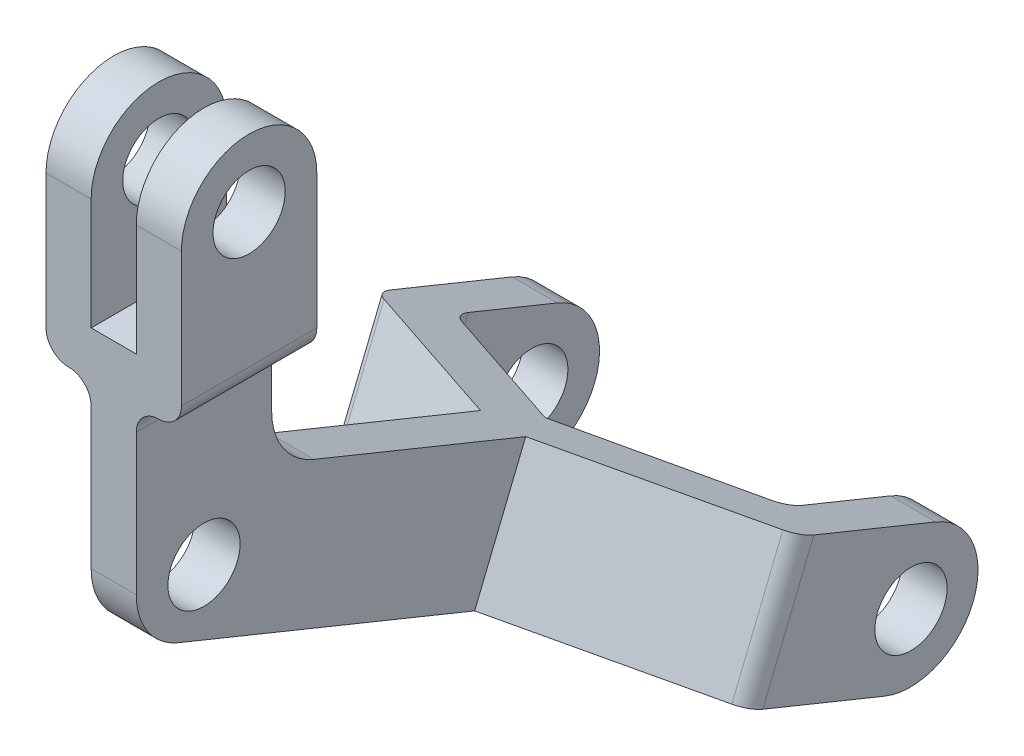
SolidWorks part; units mm, degrees
ref_plane "Front Plane" through (0, 0, 0) normal (0, 0, 1) x (1, 0, 0)
ref_plane "Top Plane" through (0, 0, 0) normal (0, 1, 0) x (1, 0, 0)
ref_plane "Right Plane" through (0, 0, 0) normal (1, 0, 0) x (0, 0, -1)
sketch "Sketch1" plane through (0, 0, 0) normal (1, 0, 0) x (0, 0, -1)
  line L0 (0, 0) -> (15, 0)
  line L2 (0, 0) -> (0, -15.9)
  line L3 (0, -15.9) -> (0, -15.59)
  line L4 (4.6728, -22.5367) -> (37.4848, -35.8904)
  line L5 (37.4848, -35.8904) -> (43.1391, -21.997)
  line L6 (43.1391, -21.997) -> (19.6728, -12.4467)
  line L8 (15, 0) -> (15, -5.5)
  arc A0 (0, -15.59) -> (4.6728, -22.5367) centre (7.5, -15.59) ccw
  arc A1 (19.6728, -12.4467) -> (15, -5.5) centre (22.5, -5.5) cw
  circle A2 centre (7.5, -16.4624) radius 4
  dimension "D3" = 7.5
  dimension "D4" = 7.5
  dimension "D9" = 8
  dimension "D1" = 15
  dimension "D2" = 15
  dimension "D5" = 5.5
  dimension "D6" = 15.59
  dimension "D7" = 6.7
  dimension "D8" = 7.5
extrude "Boss-Extrude1" add sketch "Sketch1" along normal blind 5 contours L6 A1 L8 L0 L2 A0 L4 L5 A2
sketch "Sketch2" plane through (0, 0, 0) normal (0, 0, 1) x (1, 0, 0)
  line L0 (0, 0) -> (5, 0)
  line L1 (5, 0) -> (5, -15.59) construction
  line L2 (10, 5) -> (10, 19.86)
  line L3 (10, 19.86) -> (5, 19.86)
  line L4 (5, 19.86) -> (5, 7.5)
  line L5 (5, 7.5) -> (0, 7.5)
  line L6 (0, 19.86) -> (0, 7.5)
  line L7 (2.5, 0) -> (2.5, 22.7767) construction
  line L8 (-5, 19.86) -> (0, 19.86)
  line L9 (-5, 5) -> (-5, 19.86)
  arc A0 (5, 0) -> (7.5, 2.5) centre (7.5, 0) cw
  arc A1 (7.5, 2.5) -> (10, 5) centre (7.5, 5) ccw
  arc A2 (-2.5, 2.5) -> (-5, 5) centre (-2.5, 5) cw
  arc A3 (0, 0) -> (-2.5, 2.5) centre (-2.5, 0) ccw
  point P22 (2.5, 7.5)
  dimension "D4" = 2.5
  dimension "D5" = 2.5
  dimension "D1" = 2.5
  dimension "D2" = 5
  dimension "D3" = 14.86
  dimension "D6" = 12.36
extrude "Boss-Extrude2" add sketch "Sketch2" against normal up to surface (15 mm away) up to face at (2.5, -2.75, -15)
sketch "Sketch3" plane through (10, 0, 0) normal (1, 0, 0) x (0, 0, -1)
  line L0 (0, 19.86) -> (27.8005, 19.86) construction
  line L2 (7.5, 5) -> (7.5, 19.86) construction
  line L3 (15, 5) -> (0, 5) construction
  circle A0 centre (7.5, 19.86) radius 7.5
  circle A1 centre (7.5, 19.86) radius 4
  dimension "D1" = 8
extrude "Boss-Extrude3" add sketch "Sketch3" against normal up to surface (5 mm away) up to face at (5, 13.68, -7.5)
sketch "Sketch5" plane through (10, 0, 0) normal (1, 0, 0) x (0, 0, -1)
  line L0 (11.5, 19.86) -> (3.5, 19.86) construction
  circle A0 centre (7.5, 19.86) radius 4
extrude "Cut-Extrude1" cut sketch "Sketch5" against normal blind 5
sketch "Sketch6" plane through (-5, 0, 0) normal (-1, 0, 0) x (0, 0, 1)
  line L0 (-15, 19.86) -> (0, 19.86) construction
  circle A0 centre (-7.5, 19.86) radius 7.5
extrude "Boss-Extrude4" add sketch "Sketch6" against normal up to surface (5 mm away) up to face at (0, 13.68, -7.5)
sketch "Sketch7" plane through (-5, 0, 0) normal (-1, 0, 0) x (0, 0, 1)
  circle A0 centre (-7.5, 19.86) radius 4
extrude "Cut-Extrude2" cut sketch "Sketch7" against normal blind 5
sketch "Sketch8" plane through (0, -3.8094, 1.5503) normal (0, 0.9262, -0.377) x (1, 0, 0)
  line L0 (0, 48.2487) -> (5, 48.2487)
  line L2 (0, 48.2487) -> (-19.6852, 57.9592)
  line L3 (-21.0793, 60.2013) -> (-21.0793, 74.7913)
  line L4 (-21.0793, 74.7913) -> (-16.0793, 74.7913)
  line L5 (-16.0793, 74.7913) -> (-16.0793, 64.1288)
  line L6 (-14.6852, 61.8867) -> (2.2583, 53.5287)
  line L7 (19.5563, 61.9014) -> (2.2583, 53.5287)
  line L8 (20.9211, 74.713) -> (20.9211, 64.1288)
  line L9 (25.9211, 74.713) -> (20.9211, 74.713)
  line L10 (25.9211, 60.123) -> (25.9211, 74.713)
  line L11 (5, 48.2487) -> (24.5563, 57.8956)
  arc A0 (-19.6852, 57.9592) -> (-21.0793, 60.2013) centre (-18.5793, 60.2013) cw
  arc A1 (-16.0793, 64.1288) -> (-14.6852, 61.8867) centre (-13.5793, 64.1288) ccw
  arc A2 (20.9211, 64.1288) -> (19.5563, 61.9014) centre (18.4211, 64.1288) cw
  arc A3 (24.5563, 57.8956) -> (25.9211, 60.123) centre (23.4211, 60.123) ccw
  dimension "D4" = 2.5
  dimension "D5" = 2.5
  dimension "D1" = 5
  dimension "D2" = 14.59
  dimension "D3" = 21.95
  dimension "D6" = 5.28
extrude "Boss-Extrude5" add sketch "Sketch8" against normal up to surface (15 mm away) up to face at (2.5, -29.2136, -21.0788)
sketch "Sketch9" plane through (25.9211, 0, 0) normal (1, 0, 0) x (0, 0, -1)
  line L0 (61.9969, -45.8663) -> (67.6512, -31.9728) construction
  circle A0 centre (64.824, -38.9196) radius 7.5
extrude "Boss-Extrude6" add sketch "Sketch9" against normal up to surface (5 mm away) up to face at (20.9211, -36.9247, -59.9223)
sketch "Sketch10" plane through (-21.0793, 0, 0) normal (-1, 0, 0) x (0, 0, 1)
  line L0 (-62.0694, -45.8958) -> (-67.7237, -32.0023) construction
  circle A0 centre (-64.8965, -38.9491) radius 7.5
extrude "Boss-Extrude7" add sketch "Sketch10" against normal up to surface (5 mm away) up to face at (-16.0793, -36.9394, -59.9586)
sketch "Sketch11" plane through (25.9211, 0, 0) normal (1, 0, 0) x (0, 0, -1)
  circle A0 centre (64.8965, -38.9491) radius 4
  dimension "D1" = 8
extrude "Cut-Extrude3" cut sketch "Sketch11" against normal blind 64
